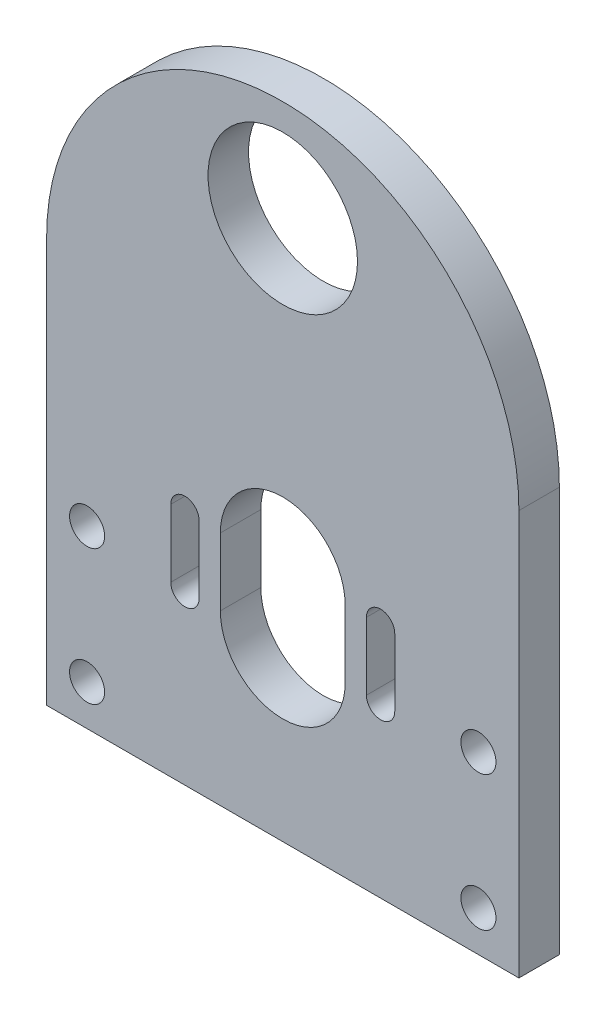
SolidWorks part; units mm, degrees
ref_plane "Ön Düzlem" through (0, 0, 0) normal (0, 0, 1) x (1, 0, 0)
ref_plane "Üst Düzlem" through (0, 0, 0) normal (0, 1, 0) x (1, 0, 0)
ref_plane "Sağ Düzlem" through (0, 0, 0) normal (1, 0, 0) x (0, 0, -1)
sketch "Çizim1" plane through (0, 0, 0) normal (0, 0, 1) x (1, 0, 0)
  line L0 (-21.4104, 4.6521) -> (-21.4104, -5.3479) construction
  line L2 (-56.4104, 29.6521) -> (-56.4104, -30.3479)
  line L3 (-56.4104, -30.3479) -> (13.5896, -30.3479)
  line L4 (13.5896, 29.6521) -> (13.5896, -30.3479)
  line L5 (-12.1604, 4.6521) -> (-12.1604, -5.3479)
  line L6 (-30.6604, 4.6521) -> (-30.6604, -5.3479)
  line L7 (-35.9104, 4.6521) -> (-35.9104, -5.3479) construction
  line L8 (-33.8104, 4.6521) -> (-33.8104, -5.3479)
  line L9 (-38.0104, 4.6521) -> (-38.0104, -5.3479)
  line L10 (-6.9104, 4.6521) -> (-6.9104, -5.3479) construction
  line L11 (-4.8104, 4.6521) -> (-4.8104, -5.3479)
  line L12 (-9.0104, 4.6521) -> (-9.0104, -5.3479)
  circle A0 centre (-21.4104, 49.6521) radius 11.075
  circle A1 centre (-50.4104, -24.3479) radius 2.6
  circle A2 centre (7.5896, -24.3479) radius 2.6
  circle A3 centre (-50.4104, -4.3479) radius 2.6
  circle A4 centre (7.5896, -4.3479) radius 2.6
  arc A5 (-12.1604, 4.6521) -> (-30.6604, 4.6521) centre (-21.4104, 4.6521) ccw
  arc A6 (-30.6604, -5.3479) -> (-12.1604, -5.3479) centre (-21.4104, -5.3479) ccw
  arc A7 (-33.8104, 4.6521) -> (-38.0104, 4.6521) centre (-35.9104, 4.6521) ccw
  arc A8 (-38.0104, -5.3479) -> (-33.8104, -5.3479) centre (-35.9104, -5.3479) ccw
  arc A9 (-4.8104, 4.6521) -> (-9.0104, 4.6521) centre (-6.9104, 4.6521) ccw
  arc A10 (-9.0104, -5.3479) -> (-4.8104, -5.3479) centre (-6.9104, -5.3479) ccw
  arc A13 (13.5896, 29.6521) -> (-56.4104, 29.6521) centre (-21.4104, 29.6521) ccw
  point P16 (-21.4104, -0.3479)
  point P23 (-35.9104, -0.3479)
  point P28 (-6.9104, -0.3479)
  point P37 (23.5896, 59.6521)
  point P40 (-56.4104, 59.6521)
  dimension "D1" = 22.15
  dimension "D5" = 5.2
  dimension "D7" = 5.2
  dimension "D11" = 35
  dimension "D13" = 9.25
  dimension "D16" = 2.1
  dimension "D17" = 2.1
  dimension "D12" = 5.2
  dimension "D2" = 80
  dimension "D3" = 70
  dimension "D4" = 6
  dimension "D6" = 6
  dimension "D8" = 6
  dimension "D9" = 6
  dimension "D14" = 14.5
  dimension "D15" = 14.5
  dimension "D18" = 0
  dimension "D19" = 0
  dimension "D20" = 0
  dimension "D21" = 10
  dimension "D22" = 10
  dimension "D23" = 30
  dimension "D10" = 2
extrude "Yükseklik-Ekstrüzyon2" add sketch "Çizim1" along normal blind 6 contours A13 L2 L3 L4 | L6 A6 L5 A5 | L12 A10 L11 A9 | L9 A8 L8 A7 | A3 | A4 | A0 | A2 | A1
